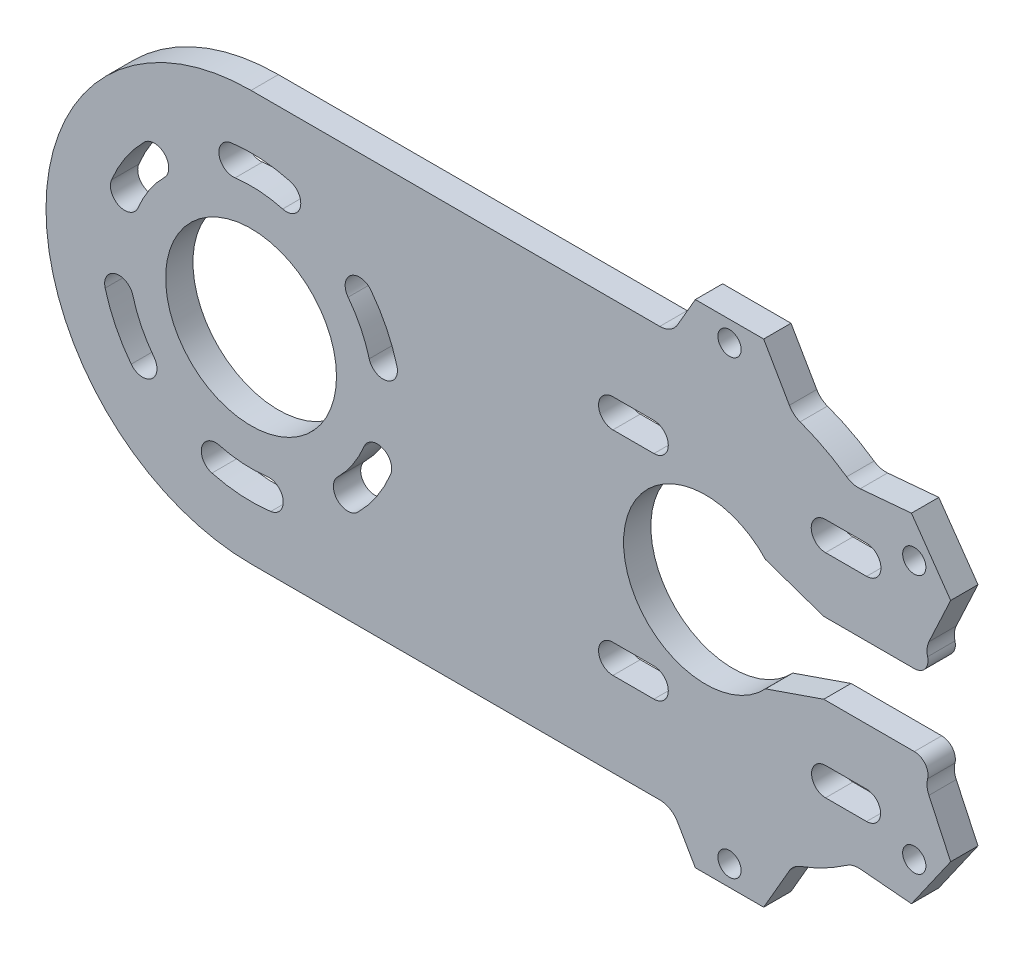
SolidWorks part; units mm, degrees
material "7075-T6 (SN)"
ref_plane "Ebene vorne" through (0, 0, 0) normal (0, 0, 1) x (1, 0, 0)
ref_plane "Ebene oben" through (0, 0, 0) normal (0, 1, 0) x (1, 0, 0)
ref_plane "Ebene rechts" through (0, 0, 0) normal (1, 0, 0) x (0, 0, -1)
sketch "Skizze1" plane through (0, 0, 0) normal (0, 0, 1) x (1, 0, 0)
  line L0 (60.6188, -25.1224) -> (53.122, -24.4665)
  line L1 (42.7599, -29.8607) -> (38.9972, -36.3779)
  line L2 (38.9972, -36.3779) -> (28.9972, -36.3779)
  line L3 (28.9972, -36.3779) -> (26.3991, -31.8779)
  line L4 (23.801, -30.3779) -> (-36.0028, -30.3779)
  line L5 (-36.0028, 29.6221) -> (23.801, 29.6221)
  line L6 (26.3991, 31.1221) -> (28.9972, 35.6221)
  line L7 (28.9972, 35.6221) -> (38.9972, 35.6221)
  line L8 (38.9972, 35.6221) -> (42.7599, 29.1049)
  line L9 (53.122, 23.7107) -> (60.6188, 24.3666)
  line L10 (60.6188, 24.3666) -> (66.3546, 16.1751)
  line L11 (66.3546, 16.1751) -> (63.1738, 9.3539)
  line L12 (61.0423, 4.8721) -> (47.7853, 4.8721)
  line L13 (47.7853, 4.8721) -> (39.265, 7.8151)
  line L14 (39.265, -8.5709) -> (47.7853, -5.6279)
  line L15 (47.7853, -5.6279) -> (61.0423, -5.6279)
  line L16 (63.1738, -10.1097) -> (66.3546, -16.9309)
  line L17 (66.3546, -16.9309) -> (60.6188, -25.1224)
  line L18 (54.0535, -13.8842) -> (48.0535, -13.8842) construction
  line L19 (48.0535, -17.9842) -> (54.0535, -17.9842) construction
  line L20 (22.9409, -13.8342) -> (16.9409, -13.8342) construction
  line L21 (16.9409, -18.0342) -> (22.9409, -18.0342) construction
  line L22 (54.0535, 17.2785) -> (48.0535, 17.2785) construction
  line L23 (48.0535, 13.0785) -> (54.0535, 13.0785) construction
  line L24 (22.9409, 17.2785) -> (16.9409, 17.2785) construction
  line L25 (16.9409, 13.0785) -> (22.9409, 13.0785) construction
  arc A0 (53.122, -24.4665) -> (51.1457, -24.9935) centre (52.8605, -27.4551) ccw
  arc A1 (44.3252, -28.544) -> (51.1457, -24.9935) centre (33.9972, -0.3779) ccw
  arc A2 (44.3252, -28.544) -> (42.7599, -29.8607) centre (45.358, -31.3607) ccw
  arc A3 (26.3991, -31.8779) -> (23.801, -30.3779) centre (23.801, -33.3779) ccw
  arc A4 (-36.0028, 29.6221) -> (-36.0028, -30.3779) centre (-36.0028, -0.3779) ccw
  arc A5 (23.801, 29.6221) -> (26.3991, 31.1221) centre (23.801, 32.6221) ccw
  arc A6 (42.7599, 29.1049) -> (44.3252, 27.7883) centre (45.358, 30.6049) ccw
  arc A7 (51.1457, 24.2378) -> (44.3252, 27.7883) centre (33.9972, -0.3779) ccw
  arc A8 (51.1457, 24.2378) -> (53.122, 23.7107) centre (52.8605, 26.6993) ccw
  arc A9 (63.1738, 9.3539) -> (62.9825, 7.3577) centre (65.8927, 8.086) ccw
  arc A10 (61.0423, 4.8721) -> (62.9825, 7.3577) centre (61.0423, 6.8721) ccw
  arc A11 (39.265, 7.8151) -> (39.265, -8.5709) centre (30.4972, -0.3779) ccw
  arc A12 (62.9825, -8.1135) -> (61.0423, -5.6279) centre (61.0423, -7.6279) ccw
  arc A13 (62.9825, -8.1135) -> (63.1738, -10.1097) centre (65.8927, -8.8418) ccw
  circle A14 centre (61.0292, -19.3059) radius 1.6 construction
  circle A15 centre (33.9972, -33.3779) radius 1.6 construction
  arc A16 (48.0535, -13.8842) -> (48.0535, -17.9842) centre (48.0535, -15.9342) ccw construction
  arc A17 (54.0535, -17.9842) -> (54.0535, -13.8842) centre (54.0535, -15.9342) ccw construction
  arc A18 (16.9409, -13.8342) -> (16.9409, -18.0342) centre (16.9409, -15.9342) ccw construction
  arc A19 (22.9409, -18.0342) -> (22.9409, -13.8342) centre (22.9409, -15.9342) ccw construction
  arc A20 (-40.6357, -17.668) -> (-33.6664, -18.1248) centre (-36.0028, -0.3779) ccw construction
  arc A21 (-40.6357, -17.668) -> (-41.7227, -21.7248) centre (-41.1792, -19.6964) ccw construction
  arc A22 (-41.7227, -21.7248) -> (-33.1182, -22.2888) centre (-36.0028, -0.3779) ccw construction
  arc A23 (-33.1182, -22.2888) -> (-33.6664, -18.1248) centre (-33.3923, -20.2068) ccw construction
  arc A24 (-20.3757, -16.0049) -> (-15.5851, -8.8352) centre (-36.0028, -0.3779) ccw construction
  arc A25 (-15.5851, -8.8352) -> (-19.4654, -7.2279) centre (-17.5252, -8.0316) ccw construction
  arc A26 (-23.3456, -13.0351) -> (-19.4654, -7.2279) centre (-36.0028, -0.3779) ccw construction
  arc A27 (-23.3456, -13.0351) -> (-20.3757, -16.0049) centre (-21.8607, -14.52) ccw construction
  arc A28 (-53.5359, -13.8315) -> (-50.2038, -11.2747) centre (-51.8699, -12.5531) ccw construction
  arc A29 (-53.2929, -5.0107) -> (-50.2038, -11.2747) centre (-36.0028, -0.3779) ccw construction
  arc A30 (-53.2929, -5.0107) -> (-57.3498, -6.0978) centre (-55.3213, -5.5543) ccw construction
  arc A31 (-57.3498, -6.0978) -> (-53.5359, -13.8315) centre (-36.0028, -0.3779) ccw construction
  circle A32 centre (-36.0028, -0.3779) radius 12.5
  circle A33 centre (61.0292, 18.5501) radius 1.6 construction
  circle A34 centre (33.9972, 32.6221) radius 1.6 construction
  arc A35 (-14.6558, 5.342) -> (-18.4697, 13.0757) centre (-36.0028, -0.3779) ccw construction
  arc A36 (-18.4697, 13.0757) -> (-21.8018, 10.5189) centre (-20.1357, 11.7973) ccw construction
  arc A37 (-18.7127, 4.255) -> (-21.8018, 10.5189) centre (-36.0028, -0.3779) ccw construction
  arc A38 (-18.7127, 4.255) -> (-14.6558, 5.342) centre (-16.6843, 4.7985) ccw construction
  arc A39 (48.0535, 17.2785) -> (48.0535, 13.0785) centre (48.0535, 15.1785) ccw construction
  arc A40 (54.0535, 13.0785) -> (54.0535, 17.2785) centre (54.0535, 15.1785) ccw construction
  arc A41 (16.9409, 17.2785) -> (16.9409, 13.0785) centre (16.9409, 15.1785) ccw construction
  arc A42 (22.9409, 13.0785) -> (22.9409, 17.2785) centre (22.9409, 15.1785) ccw construction
  arc A43 (-48.66, 12.2793) -> (-52.5402, 6.4721) centre (-36.0028, -0.3779) ccw construction
  arc A44 (-48.66, 12.2793) -> (-51.6299, 15.2492) centre (-50.1449, 13.7642) ccw construction
  arc A45 (-51.6299, 15.2492) -> (-56.4205, 8.0794) centre (-36.0028, -0.3779) ccw construction
  arc A46 (-56.4205, 8.0794) -> (-52.5402, 6.4721) centre (-54.4804, 7.2758) ccw construction
  arc A47 (-38.8874, 21.533) -> (-38.3392, 17.369) centre (-38.6133, 19.451) ccw construction
  arc A48 (-31.3699, 16.9122) -> (-38.3392, 17.369) centre (-36.0028, -0.3779) ccw construction
  arc A49 (-31.3699, 16.9122) -> (-30.2829, 20.9691) centre (-30.8264, 18.9406) ccw construction
  arc A50 (-30.2829, 20.9691) -> (-38.8874, 21.533) centre (-36.0028, -0.3779) ccw construction
extrude "Aufsatz-Linear austragen1" add sketch "Skizze1" along normal blind 4
hole_wizard "Durchgangsloch für M31" positions "Skizze2" profile "Skizze3" hole size "M3" standard "DIN" end condition through all
sketch "Skizze2" plane through (0, 0, 4) normal (0, 0, 1) x (1, 0, 0)
  point P0 (33.9972, 32.6221)
  point P3 (61.0292, 18.5501)
  point P6 (61.0292, -19.3059)
  point P9 (33.9972, -33.3779)
sketch "Skizze3" plane through (33.9972, 32.6221, 4) normal (1, 0, 0) x (0, -1, 0)
  line L0 (0, 0) -> (0, 4)
  line L1 (0, 4) -> (1.7, 4)
  line L2 (1.7, 4) -> (1.7, 0)
  line L5 (1.7, 0) -> (0, 0)
  line L11 (0, -6.35) -> (0, 107.95) construction
  dimension "Bohrerdurchmesser" = 3.4
  dimension "Bohrungstiefe" = 4
sketch "Skizze6" plane through (0, 0, 4) normal (0, 0, 1) x (1, 0, 0)
  arc A1 (-38.6133, 19.451) -> (-30.8264, 18.9406) centre (-36.0028, -0.3779) cw construction
  arc A2 (-30.2829, 20.9691) -> (-38.8874, 21.533) centre (-36.0028, -0.3779) ccw
  arc A3 (-31.3699, 16.9122) -> (-38.3392, 17.369) centre (-36.0028, -0.3779) ccw
  arc A4 (-31.3699, 16.9122) -> (-30.2829, 20.9691) centre (-30.8264, 18.9406) ccw
  arc A5 (-38.8874, 21.533) -> (-38.3392, 17.369) centre (-38.6133, 19.451) ccw
  arc A6 (-38.8874, 21.533) -> (-38.3392, 17.369) centre (-38.6133, 19.451) ccw construction
  circle A7 centre (-36.0028, -0.3779) radius 20 construction
  arc A8 (-20.1357, 11.7973) -> (-16.6843, 4.7985) centre (-36.0028, -0.3779) cw construction
  arc A9 (-14.6558, 5.342) -> (-18.4697, 13.0757) centre (-36.0028, -0.3779) ccw
  arc A10 (-18.7127, 4.255) -> (-21.8018, 10.5189) centre (-36.0028, -0.3779) ccw
  arc A11 (-18.7127, 4.255) -> (-14.6558, 5.342) centre (-16.6843, 4.7985) ccw
  arc A12 (-18.4697, 13.0757) -> (-21.8018, 10.5189) centre (-20.1357, 11.7973) ccw
  arc A13 (-17.5252, -8.0316) -> (-21.8607, -14.52) centre (-36.0028, -0.3779) cw construction
  arc A14 (-20.3757, -16.0049) -> (-15.5851, -8.8352) centre (-36.0028, -0.3779) ccw
  arc A15 (-23.3456, -13.0351) -> (-19.4654, -7.2279) centre (-36.0028, -0.3779) ccw
  arc A16 (-23.3456, -13.0351) -> (-20.3757, -16.0049) centre (-21.8607, -14.52) ccw
  arc A17 (-15.5851, -8.8352) -> (-19.4654, -7.2279) centre (-17.5252, -8.0316) ccw
  arc A18 (-33.3923, -20.2068) -> (-41.1792, -19.6964) centre (-36.0028, -0.3779) cw construction
  arc A19 (-41.7227, -21.7248) -> (-33.1182, -22.2888) centre (-36.0028, -0.3779) ccw
  arc A20 (-40.6357, -17.668) -> (-33.6664, -18.1248) centre (-36.0028, -0.3779) ccw
  arc A21 (-40.6357, -17.668) -> (-41.7227, -21.7248) centre (-41.1792, -19.6964) ccw
  arc A22 (-33.1182, -22.2888) -> (-33.6664, -18.1248) centre (-33.3923, -20.2068) ccw
  arc A23 (-51.8699, -12.5531) -> (-55.3213, -5.5543) centre (-36.0028, -0.3779) cw construction
  arc A24 (-57.3498, -6.0978) -> (-53.5359, -13.8315) centre (-36.0028, -0.3779) ccw
  arc A25 (-53.2929, -5.0107) -> (-50.2038, -11.2747) centre (-36.0028, -0.3779) ccw
  arc A26 (-53.2929, -5.0107) -> (-57.3498, -6.0978) centre (-55.3213, -5.5543) ccw
  arc A27 (-53.5359, -13.8315) -> (-50.2038, -11.2747) centre (-51.8699, -12.5531) ccw
  arc A28 (-54.4804, 7.2758) -> (-50.1449, 13.7642) centre (-36.0028, -0.3779) cw construction
  arc A29 (-51.6299, 15.2492) -> (-56.4205, 8.0794) centre (-36.0028, -0.3779) ccw
  arc A30 (-48.66, 12.2793) -> (-52.5402, 6.4721) centre (-36.0028, -0.3779) ccw
  arc A31 (-48.66, 12.2793) -> (-51.6299, 15.2492) centre (-50.1449, 13.7642) ccw
  arc A32 (-56.4205, 8.0794) -> (-52.5402, 6.4721) centre (-54.4804, 7.2758) ccw
  point P5 (-34.6947, 19.5793)
  point P21 (-18.0653, 8.4679)
  point P28 (-19.3734, -11.4893)
  point P35 (-37.3109, -20.3351)
  point P42 (-53.9403, -9.2237)
  point P49 (-52.6322, 10.7335)
  point P54 (-36.0028, -0.3779)
  dimension "D1" = 6
extrude "Schnitt-Linear austragen1" cut sketch "Skizze6" against normal through all
sketch "Skizze7" plane through (0, 0, 4) normal (0, 0, 1) x (1, 0, 0)
  line L0 (16.9409, 15.1785) -> (22.9409, 15.1785) construction
  line L1 (16.9409, 17.2785) -> (22.9409, 17.2785)
  line L2 (16.9409, 13.0785) -> (22.9409, 13.0785)
  line L3 (48.0535, 15.1785) -> (54.0535, 15.1785) construction
  line L4 (48.0535, 17.2785) -> (54.0535, 17.2785)
  line L5 (48.0535, 13.0785) -> (54.0535, 13.0785)
  line L6 (54.0535, -15.9342) -> (48.0535, -15.9342) construction
  line L7 (54.0535, -17.9842) -> (48.0535, -17.9842)
  line L8 (54.0535, -13.8842) -> (48.0535, -13.8842)
  line L9 (22.9409, -15.9342) -> (16.9409, -15.9342) construction
  line L10 (22.9409, -18.0342) -> (16.9409, -18.0342)
  line L11 (22.9409, -13.8342) -> (16.9409, -13.8342)
  arc A0 (16.9409, 17.2785) -> (16.9409, 13.0785) centre (16.9409, 15.1785) ccw
  arc A1 (22.9409, 13.0785) -> (22.9409, 17.2785) centre (22.9409, 15.1785) ccw
  arc A2 (48.0535, 17.2785) -> (48.0535, 13.0785) centre (48.0535, 15.1785) ccw
  arc A3 (54.0535, 13.0785) -> (54.0535, 17.2785) centre (54.0535, 15.1785) ccw
  arc A4 (54.0535, -17.9842) -> (54.0535, -13.8842) centre (54.0535, -15.9342) ccw
  arc A5 (48.0535, -13.8842) -> (48.0535, -17.9842) centre (48.0535, -15.9342) ccw
  arc A6 (22.9409, -18.0342) -> (22.9409, -13.8342) centre (22.9409, -15.9342) ccw
  arc A7 (16.9409, -13.8342) -> (16.9409, -18.0342) centre (16.9409, -15.9342) ccw
  arc A8 (16.9409, -13.8342) -> (16.9409, -18.0342) centre (16.9409, -15.9342) ccw construction
  arc A9 (16.9409, 17.2785) -> (16.9409, 13.0785) centre (16.9409, 15.1785) ccw construction
  arc A10 (48.0535, 17.2785) -> (48.0535, 13.0785) centre (48.0535, 15.1785) ccw construction
  arc A11 (48.0535, -13.8842) -> (48.0535, -17.9842) centre (48.0535, -15.9342) ccw construction
  point P4 (19.9409, 15.1785)
  point P13 (51.0535, 15.1785)
  point P18 (51.0535, -15.9342)
  point P27 (19.9409, -15.9342)
extrude "Schnitt-Linear austragen2" cut sketch "Skizze7" against normal through all
